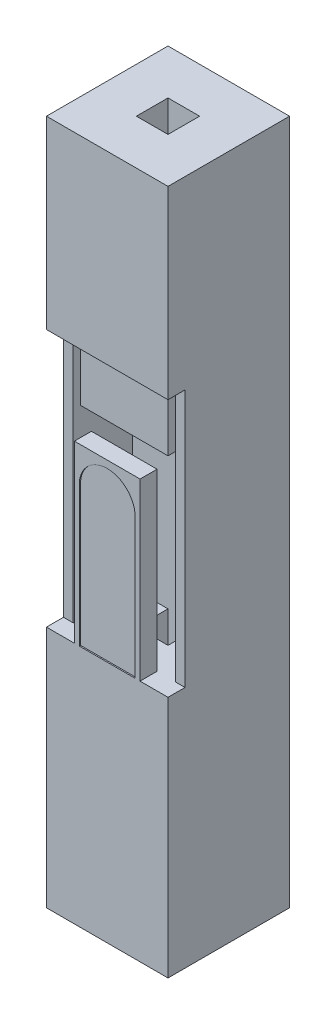
SolidWorks part; units mm, degrees
other "Camera1"
material "Nylon 101"
ref_plane "Front Plane" through (0, 0, 0) normal (0, 0, 1) x (1, 0, 0)
ref_plane "Top Plane" through (0, 0, 0) normal (0, 1, 0) x (1, 0, 0)
ref_plane "Right Plane" through (0, 0, 0) normal (1, 0, 0) x (0, 0, -1)
sketch "Sketch2" plane through (0, 0, 0) normal (0, 1, 0) x (1, 0, 0)
  line L1 (-1.25, -1.25) -> (1.25, -1.25)
  line L2 (-1.25, -1.25) -> (-1.25, 1.25)
  line L3 (-1.25, 1.25) -> (1.25, 1.25)
  line L4 (1.25, -1.25) -> (1.25, 1.25)
  line L5 (-1.25, -1.25) -> (1.25, 1.25) construction
  line L6 (-1.25, 1.25) -> (1.25, -1.25) construction
  point P0 (0, 0)
  dimension "D1" = 2.5
extrude "Boss-Extrude1" add sketch "Sketch2" along normal mid plane 14.1
sketch "Sketch3" plane through (0, 7.05, 0) normal (0, 1, 0) x (1, 0, 0)
  line L1 (0.325, -0.325) -> (-0.325, -0.325)
  line L2 (0.325, -0.325) -> (0.325, 0.325)
  line L3 (0.325, 0.325) -> (-0.325, 0.325)
  line L4 (-0.325, -0.325) -> (-0.325, 0.325)
  line L5 (0.325, -0.325) -> (-0.325, 0.325) construction
  line L6 (0.325, 0.325) -> (-0.325, -0.325) construction
  point P0 (0, 0)
  dimension "D1" = 0.65
extrude "Pinhole" cut sketch "Sketch3" against normal up to next
sketch "Sketch4" plane through (0, 0, 1.25) normal (0, 0, 1) x (1, 0, 0)
  line L0 (-1.25, 7.05) -> (-1.25, -7.05) construction
  line L1 (-1.25, 3.25) -> (1.25, 3.25)
  line L2 (-1.25, 3.25) -> (-1.25, -2.05)
  line L3 (-1.25, -2.05) -> (-0.675, -2.05)
  line L4 (1.25, 3.25) -> (1.25, -2.05)
  line L5 (0.675, -2.05) -> (1.25, -2.05)
  line L6 (-0.675, -2.05) -> (0.675, -2.05) construction
  line L7 (1.25, 7.05) -> (1.25, -7.05) construction
  line L8 (-1.25, 7.05) -> (1.25, 7.05) construction
  line L9 (-1.25, -7.05) -> (1.25, -7.05) construction
  line L10 (-0.675, -2.05) -> (-0.675, 1.55)
  line L11 (-0.675, 1.55) -> (0.675, 1.55)
  line L12 (0.675, -2.05) -> (0.675, 1.55)
  dimension "D1" = 3.8
  dimension "D2" = 5
  dimension "D3" = 1.35
  dimension "D4" = 3.6
extrude "Cut-Extrude2" cut sketch "Sketch4" against normal blind 0.35
sketch "Sketch5" plane through (0, 0, 0.9) normal (0, 0, 1) x (1, 0, 0)
  line L0 (-1.25, 7.05) -> (1.25, 7.05) construction
  line L1 (-1.05, 3.25) -> (1.05, 3.25)
  line L2 (-1.05, 3.25) -> (-1.05, -2.05)
  line L3 (-1.05, -2.05) -> (1.05, -2.05)
  line L4 (1.05, 3.25) -> (1.05, -2.05)
  line L5 (-1.05, 3.25) -> (1.05, -2.05) construction
  line L6 (-1.05, -2.05) -> (1.05, 3.25) construction
  line L7 (0.675, -2.05) -> (1.25, -2.05) construction
  line L8 (-1.25, 3.25) -> (-1.25, -2.05) construction
  line L9 (1.25, 3.25) -> (-1.25, 3.25) construction
  point P4 (0, 0.6)
  point P5 (0, 3.25)
  point P8 (0, 7.05)
  dimension "D1" = 0.2
extrude "Cut-Extrude3" cut sketch "Sketch5" against normal up to surface (1.225 mm away) up to face at (0, 0, -0.325)
sketch "Sketch6" plane through (0, 0, 1.25) normal (0, 0, 1) x (1, 0, 0)
  line L0 (-0.575, -2.05) -> (-0.575, 0.825)
  line L1 (-0.675, -2.05) -> (-0.675, 1.55) construction
  line L2 (-0.6875, -2.05) -> (0.6875, -2.05)
  line L3 (-1.05, -2.05) -> (-0.325, -2.05) construction
  line L4 (0.325, -2.05) -> (1.05, -2.05) construction
  line L5 (0, 1.55) -> (0, -2.05) construction
  line L6 (-0.675, 1.55) -> (0.675, 1.55) construction
  line L7 (0.575, -2.05) -> (0.575, 0.825)
  arc A0 (-0.575, 0.825) -> (0.575, 0.825) centre (0, 0.825) cw
  point P17 (0, 1.4)
  dimension "D2" = 0.15
  dimension "D1" = 0.1
extrude "Cut-Extrude5" cut sketch "Sketch6" against normal blind 0.025 contours L5 A0 L0 L2 | A0 L5 L2 L7
sketch "Sketch7" plane through (0, -7.05, 0) normal (0, -1, 0) x (1, 0, 0)
  line L0 (-1.25, -1.25) -> (-1.25, 1.25) construction
  line L1 (1.05, -1.05) -> (-1.05, -1.05)
  line L2 (1.05, -1.05) -> (1.05, 1.05)
  line L3 (1.05, 1.05) -> (-1.05, 1.05)
  line L4 (-1.05, -1.05) -> (-1.05, 1.05)
  line L5 (1.05, -1.05) -> (-1.05, 1.05) construction
  line L6 (1.05, 1.05) -> (-1.05, -1.05) construction
  point P0 (0, 0)
  dimension "D1" = 0.2
extrude "Cut-Extrude6" cut sketch "Sketch7" against normal blind 4
sketch "Sketch8" [suppressed] plane through (0, -3.05, 0) normal (0, -1, 0) x (1, 0, 0)
  circle A0 centre (0, 0) radius 0.45
  circle A1 centre (0, 0) radius 0.55
  dimension "D1" = 0.9
  dimension "D2" = 0.1
extrude "Wire hole" [suppressed] add sketch "Sketch8" along normal blind 3
sketch "Sketch9" plane through (0, 0, -0.325) normal (0, 0, 1) x (1, 0, 0)
  line L1 (-0.9, 2.9) -> (-0.75, 2.9)
  line L2 (-0.9, 2.9) -> (-0.9, 1.9)
  line L3 (-0.9, 1.9) -> (-0.75, 1.9)
  line L4 (0.9, 2.9) -> (0.9, 1.9)
  line L5 (0.75, 2.9) -> (-0.75, 2.9) construction
  line L6 (0.9, 2.9) -> (0.75, 2.9)
  line L7 (-0.325, 3.25) -> (0.325, 3.25) construction
  line L8 (-0.75, 2.9) -> (-0.75, 1.9)
  line L9 (0, 2.9) -> (0, 1.9) construction
  line L10 (0.75, 2.9) -> (0.75, 1.9)
  line L11 (-1.05, 3.25) -> (-1.05, -2.05) construction
  line L12 (0, 3.25) -> (0, 2.9) construction
  line L13 (0.75, 1.9) -> (-0.75, 1.9) construction
  line L14 (0.75, 1.9) -> (0.9, 1.9)
  point P4 (0, 2.4)
  point P23 (0, 2.9)
  point P24 (0, 1.9)
  dimension "D1" = 1
  dimension "D2" = 0.15
  dimension "D3" = 0.15
  dimension "D4" = 0.85
extrude "Holder-1" add sketch "Sketch9" along normal offset from surface (1.075 mm away) 0.15 up to face at (0, -0.25, 0.9)
sketch "Sketch10" plane through (0, 0, 0.75) normal (0, 0, 1) x (1, 0, 0)
  line L1 (-0.9, 2.9) -> (0.9, 2.9)
  line L2 (-0.9, 2.9) -> (-0.9, 1.9)
  line L3 (-0.9, 1.9) -> (0.9, 1.9)
  line L4 (0.9, 2.9) -> (0.9, 1.9)
  line L5 (-0.9, 2.9) -> (0.9, 1.9) construction
  line L6 (-0.9, 1.9) -> (0.9, 2.9) construction
  point P4 (0, 2.4)
extrude "Holder-2" add sketch "Sketch10" along normal blind 0.15
ref_plane "Snap plane" through (0, 6.05, 0) normal (0, 1, 0) x (1, 0, 0)
